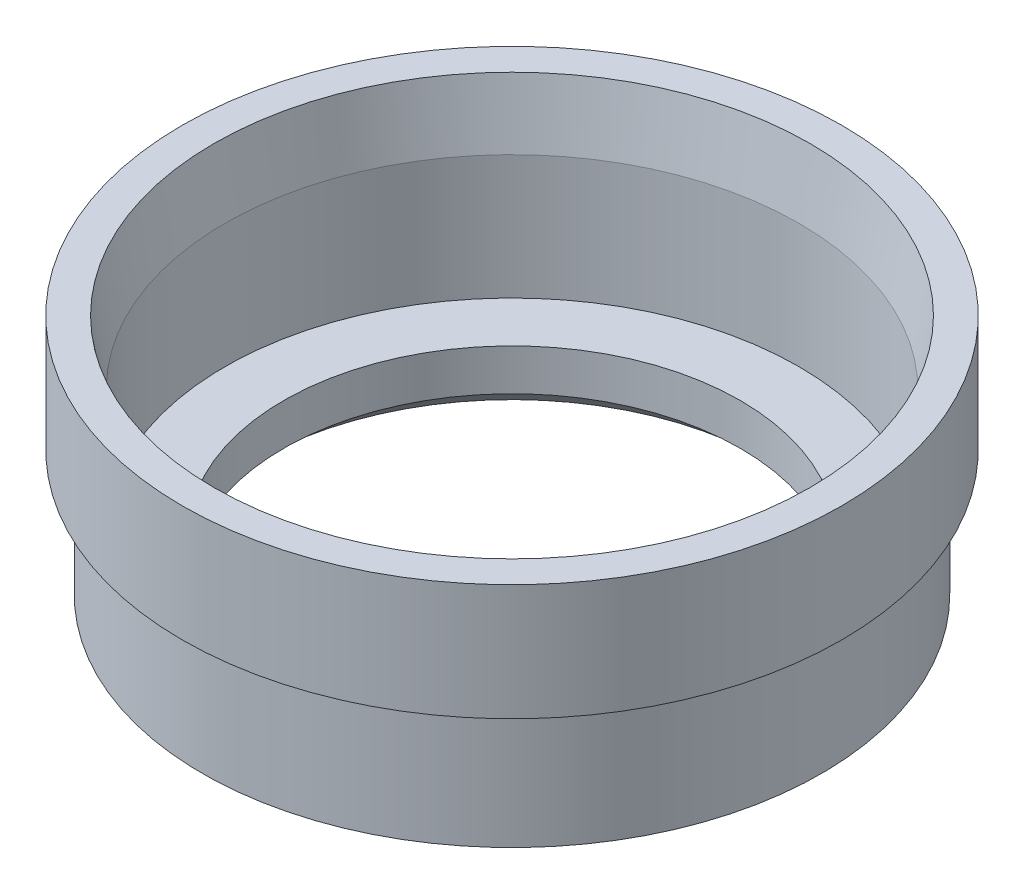
SolidWorks part; units mm, degrees
ref_plane "Front Plane" through (0, 0, 0) normal (0, 0, 1) x (1, 0, 0)
ref_plane "Top Plane" through (0, 0, 0) normal (0, 1, 0) x (1, 0, 0)
ref_plane "Right Plane" through (0, 0, 0) normal (1, 0, 0) x (0, 0, -1)
sketch "Sketch2" plane through (0, 0, 0) normal (0, 0, 1) x (1, 0, 0)
  line L0 (0, 5.2456) -> (0, 8.6395)
  line L1 (0, 8.6395) -> (4.8, 8.6395)
  line L2 (4.8, 8.6395) -> (4.8, 18.8103)
  line L3 (4.8, 18.8103) -> (5.7059, 24.0144)
  line L7 (6.65, 14.5056) -> (6.65, 4.2056)
  line L8 (6.65, 4.2056) -> (3.7962, 4.2056)
  line L9 (3.7962, 4.2056) -> (3.7962, 3.2056)
  line L10 (3.7962, 3.2056) -> (2.2962, 3.2056)
  line L11 (2.2962, 3.2056) -> (0, 5.2456)
  line L13 (-18.7, 7.4362) -> (-18.7, 16.9661)
  line L14 (6.65, 24.0144) -> (5.7059, 24.0144)
  line L15 (6.65, 14.5056) -> (8.3, 14.5056)
  line L16 (8.3, 14.5056) -> (8.3, 24.0144)
  line L17 (6.65, 24.0144) -> (8.3, 24.0144)
  dimension "D1" = 27
  dimension "D4" = 6.65
  dimension "D5" = 1.5
  dimension "D6" = 25.35
  dimension "D7" = 10.3
revolve "Revolve1" add sketch "Sketch2" angle 360 about L13
